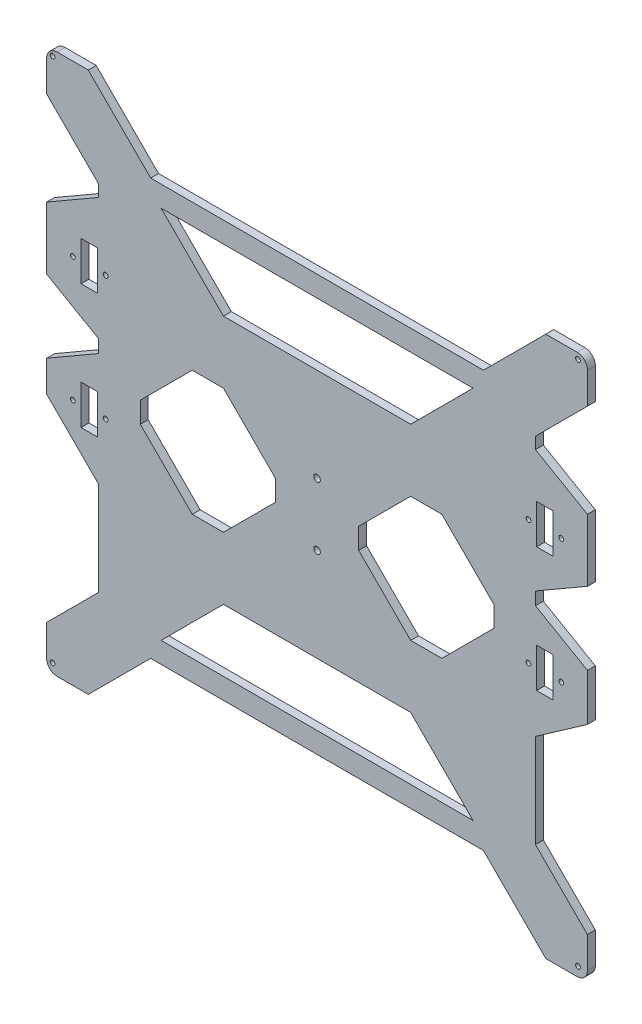
SolidWorks part; units mm, degrees
material "5052-H32"
ref_plane "Front Plane" through (0, 0, 0) normal (0, 0, 1) x (1, 0, 0)
ref_plane "Top Plane" through (0, 0, 0) normal (0, 1, 0) x (1, 0, 0)
ref_plane "Right Plane" through (0, 0, 0) normal (1, 0, 0) x (0, 0, -1)
sketch "Model" plane through (0, 0, 0) normal (0, 0, 1) x (1, 0, 0)
  line L0 (38.5361, 132.6139) -> (38.5361, 132.4727)
  line L1 (38.5361, -178.6774) -> (38.5361, -178.7219)
  line L2 (-253.5639, -197.5861) -> (-253.5639, -197.7273)
  line L3 (-290.6813, -31.2683) -> (-258.9313, -12.9374)
  line L4 (-258.9313, -82.0683) -> (-258.9313, -139.2183)
  line L5 (38.5361, 132.6139) -> (38.5361, 132.4727)
  line L6 (38.5361, -178.6774) -> (38.5361, -178.7219)
  line L7 (7.7687, -139.2183) -> (7.7687, -82.0683)
  line L8 (39.5187, -59.8367) -> (39.5187, -31.2683)
  line L9 (-23.9813, 95.7317) -> (-227.1813, 95.7317)
  line L10 (-290.6813, 108.4317) -> (-258.9313, 76.6817)
  line L11 (-30.3313, -145.5683) -> (-68.4313, -107.4683)
  line L12 (-23.9813, -158.2683) -> (14.1187, -196.3683)
  line L13 (39.5187, 108.4317) -> (39.5187, 127.4817)
  line L14 (-227.1813, 95.7317) -> (-265.2813, 133.8317)
  line L15 (-220.8313, 83.0317) -> (-182.7313, 44.9317)
  line L16 (-274.6813, -45.4288) -> (-254.6813, -45.4288) construction
  line L17 (39.5187, -170.9683) -> (7.7687, -139.2183)
  line L18 (-265.2813, -196.3683) -> (-227.1813, -158.2683)
  line L19 (-182.7313, -107.4683) -> (-68.4313, -107.4683)
  line L20 (-264.6813, -45.4288) -> (-264.6813, -43.5832) construction
  line L21 (7.7687, 76.6817) -> (39.5187, 108.4317)
  line L22 (-23.9813, 95.7317) -> (14.1187, 133.8317)
  line L23 (-30.3313, 83.0317) -> (-68.4313, 44.9317)
  line L24 (39.5187, -31.2683) -> (7.7687, -12.9374)
  line L25 (-258.9313, -139.2183) -> (-290.6813, -170.9683)
  line L26 (-182.7313, 44.9317) -> (-68.4313, 44.9317)
  line L27 (-220.8313, -145.5683) -> (-182.7313, -107.4683)
  line L28 (-220.8313, -145.5683) -> (-30.3313, -145.5683)
  line L29 (-258.9313, -82.0683) -> (-290.6813, -50.3183)
  line L30 (-290.6813, -31.2683) -> (-290.6813, -50.3183)
  line L31 (-274.6813, -43.9683) -> (-274.6813, -31.2683) construction
  line L32 (-258.9313, -12.9374) -> (-258.9313, -5.1492)
  line L33 (-201.7813, -69.3683) -> (-233.5313, -37.6183)
  line L34 (-182.7313, -69.3683) -> (-201.7813, -69.3683)
  line L35 (7.7687, -12.9374) -> (7.7687, -5.1492)
  line L36 (7.7687, -5.1492) -> (39.5187, 13.1817)
  line L37 (-150.9813, -37.6183) -> (-182.7313, -69.3683)
  line L38 (39.5187, -59.8367) -> (10.4646, -80.1806)
  line L39 (10.4646, -80.1806) -> (7.7687, -82.0683)
  line L40 (-100.1813, -37.6183) -> (-100.1813, -24.9183)
  line L41 (-150.9813, -37.6183) -> (-150.9813, -24.9183)
  line L42 (-150.9813, -24.9183) -> (-182.7313, 6.8317)
  line L43 (-182.7313, 6.8317) -> (-201.7813, 6.8317)
  line L44 (-201.7813, 6.8317) -> (-233.5313, -24.9183)
  line L45 (-233.5313, -24.9183) -> (-233.5313, -37.6183)
  line L46 (-17.6313, -24.9183) -> (-17.6313, -37.6183)
  line L47 (-49.3813, 6.8317) -> (-17.6313, -24.9183)
  line L48 (-220.8313, 83.0317) -> (-30.3313, 83.0317)
  line L49 (-68.4313, 6.8317) -> (-49.3813, 6.8317)
  line L50 (-100.1813, -24.9183) -> (-68.4313, 6.8317)
  line L51 (-100.1813, -37.6183) -> (-68.4313, -69.3683)
  line L52 (-68.4313, -69.3683) -> (-49.3813, -69.3683)
  line L53 (-49.3813, -69.3683) -> (-17.6313, -37.6183)
  line L54 (39.5187, 13.1817) -> (39.5187, 51.2817)
  line L55 (39.5187, 51.2817) -> (7.7687, 69.6126)
  line L56 (7.7687, 69.6126) -> (7.7687, 76.6817)
  line L57 (-258.9313, -5.1492) -> (-290.6813, 13.1817)
  line L58 (-265.2813, -196.3683) -> (-284.3313, -196.3683)
  line L59 (-290.6813, -190.0183) -> (-290.6813, -170.9683)
  line L60 (-290.6813, 108.4317) -> (-290.6813, 127.4817)
  line L61 (-284.3313, 133.8317) -> (-265.2813, 133.8317)
  line L62 (14.1187, 133.8317) -> (33.1687, 133.8317)
  line L63 (-290.6813, 13.1817) -> (-290.6813, 51.2817)
  line L64 (39.5187, -170.9683) -> (39.5187, -190.0183)
  line L65 (33.1687, -196.3683) -> (14.1187, -196.3683)
  line L66 (-258.9313, 76.6817) -> (-258.9313, 69.6126)
  line L67 (-258.9313, 69.6126) -> (-290.6813, 51.2817)
  line L68 (-274.6813, 30.5682) -> (-254.6813, 30.5682) construction
  line L69 (-254.6813, 30.5682) -> (23.5187, 30.5682) construction
  line L70 (23.5187, 30.5682) -> (23.5187, -45.4288) construction
  line L71 (-227.1813, -158.2683) -> (-23.9813, -158.2683)
  line L72 (38.5361, -178.6774) -> (38.5361, -178.7219)
  line L73 (3.5187, 30.5682) -> (3.5187, -45.4288) construction
  line L74 (-227.1813, -158.2683) -> (-23.9813, -158.2683)
  line L75 (38.5361, -178.6774) -> (38.5361, -178.7219)
  line L76 (-274.6813, 30.5682) -> (-274.6813, -45.4288) construction
  line L77 (-125.5813, 95.7317) -> (-125.5813, -158.2683) construction
  line L78 (-290.6813, -31.2683) -> (39.5187, -31.2683) construction
  arc A0 (33.1687, -196.3683) -> (39.5187, -190.0183) centre (33.1687, -190.0183) ccw
  arc A1 (-290.6813, -190.0183) -> (-284.3313, -196.3683) centre (-284.3313, -190.0183) ccw
  arc A2 (-290.6813, 127.4817) -> (-284.3313, 133.8317) centre (-284.3313, 127.4817) cw
  arc A3 (33.1687, 133.8317) -> (39.5187, 127.4817) centre (33.1687, 127.4817) cw
  circle A4 centre (-287.1253, -190.6025) radius 1.4605
  circle A5 centre (33.7529, -190.6025) radius 1.4605
  circle A6 centre (33.7529, 130.2757) radius 1.4605
  circle A7 centre (-287.1253, 130.2757) radius 1.4605
  circle A8 centre (-274.6813, -45.4288) radius 1.4605
  circle A9 centre (-254.6813, -45.4288) radius 1.4605
  circle A10 centre (23.5187, -45.4288) radius 1.4605
  circle A11 centre (3.5187, -45.4288) radius 1.4605
  circle A12 centre (23.5187, 30.5682) radius 1.4605
  circle A13 centre (3.5187, 30.5682) radius 1.4605
  circle A14 centre (-254.6813, 30.5682) radius 1.4605
  circle A15 centre (-274.6813, 30.5682) radius 1.4605
  circle A16 centre (-125.5813, -12.2183) radius 2
  circle A17 centre (-125.5813, -50.3183) radius 2
  point P72 (-125.5813, -31.2683)
  point P114 (-125.5813, 83.0317)
  point P120 (-233.5313, -31.2683)
  point P129 (-150.9813, -31.2683)
  point P149 (-125.5813, 44.9317)
  point P156 (-17.6313, -31.2683)
  dimension "D28" = 6.35
  dimension "D29" = 6.35
  dimension "D30" = 6.35
  dimension "D31" = 6.35
  dimension "D35" = 2.921
  dimension "D36" = 2.921
  dimension "D37" = 2.921
  dimension "D38" = 2.921
  dimension "D53" = 2.921
  dimension "D54" = 2.921
  dimension "D56" = 4
  dimension "D57" = 4
  dimension "D1" = 330.2
  dimension "D2" = 330.2
  dimension "D3" = 135
  dimension "D4" = 135
  dimension "D5" = 38.1
  dimension "D6" = 135
  dimension "D7" = 120
  dimension "D8" = 19.05
  dimension "D9" = 135
  dimension "D10" = 19.05
  dimension "D11" = 31.75
  dimension "D12" = 190.5
  dimension "D13" = 114.3
  dimension "D14" = 38.1
  dimension "D15" = 114.3
  dimension "D16" = 135
  dimension "D17" = 6.35
  dimension "D18" = 38.1
  dimension "D19" = 135
  dimension "D20" = 135
  dimension "D21" = 6.35
  dimension "D22" = 19.05
  dimension "D23" = 25.4
  dimension "D24" = 50.8
  dimension "D25" = 120
  dimension "D26" = 135
  dimension "D27" = 127
  dimension "D32" = 19.05
  dimension "D33" = 19.05
  dimension "D34" = 19.05
  dimension "D39" = 120
  dimension "D40" = 19.05
  dimension "D41" = 120
  dimension "D42" = 120
  dimension "D43" = 50.8
  dimension "D44" = 19.05
  dimension "D45" = 31.75
  dimension "D46" = 125
  dimension "D47" = 320.8782
  dimension "D48" = 320.8782
  dimension "D49" = 3.556
  dimension "D50" = 3.556
  dimension "D51" = 20
  dimension "D52" = 26
  dimension "D55" = 12.7
  dimension "D58" = 38.1
  dimension "D59" = 19.05
  dimension "D60" = 82.55
  dimension "D61" = 38.1
  dimension "D63" = 120
  dimension "D64" = 38.1
  dimension "D65" = 82.55
  dimension "D67" = 75.997
extrude "Boss-Extrude1" add sketch "Model" along normal mid plane 4.826
sketch "Sketch1" plane through (0, 0, 2.413) normal (0, 0, 1) x (1, 0, 0)
  line L0 (23.5187, 30.5682) -> (23.5187, 17.7506) construction
  line L1 (-269.6813, -33.4288) -> (-259.6813, -33.4288)
  line L2 (-269.6813, -33.4288) -> (-269.6813, -57.4288)
  line L3 (-269.6813, -57.4288) -> (-259.6813, -57.4288)
  line L4 (-259.6813, -33.4288) -> (-259.6813, -57.4288)
  line L5 (-269.6813, 42.5712) -> (-259.6813, 42.5712)
  line L6 (-269.6813, 42.5712) -> (-269.6813, 18.5712)
  line L7 (-269.6813, 18.5712) -> (-259.6813, 18.5712)
  line L8 (-259.6813, 42.5712) -> (-259.6813, 18.5712)
  line L9 (8.5187, 42.5712) -> (18.5187, 42.5712)
  line L10 (8.5187, 42.5712) -> (8.5187, 18.5712)
  line L11 (8.5187, 18.5712) -> (18.5187, 18.5712)
  line L12 (18.5187, 42.5712) -> (18.5187, 18.5712)
  line L13 (8.5187, -33.4288) -> (18.5187, -33.4288)
  line L14 (8.5187, -33.4288) -> (8.5187, -57.4288)
  line L15 (8.5187, -57.4288) -> (18.5187, -57.4288)
  line L16 (18.5187, -33.4288) -> (18.5187, -57.4288)
  circle A1 centre (-274.6813, -45.4288) radius 1.4605 construction
  circle A5 centre (-274.6813, 30.5682) radius 1.4605 construction
  circle A8 centre (23.5187, 30.5682) radius 1.4605 construction
  circle A9 centre (23.5187, -45.4288) radius 1.4605 construction
  point P20 (13.5187, 42.5712)
  dimension "D3" = 12
  dimension "D4" = 5
  dimension "D5" = 10
  dimension "D8" = 100
  dimension "D11" = 100
  dimension "D15" = 12
  dimension "D1" = 10
  dimension "D2" = 24
  dimension "D6" = 24
  dimension "D7" = 5
  dimension "D9" = 24
  dimension "D10" = 5
  dimension "D12" = 10
  dimension "D13" = 10
  dimension "D14" = 24
  dimension "D16" = 5
extrude "Cut-Extrude1" cut sketch "Sketch1" against normal blind 10
